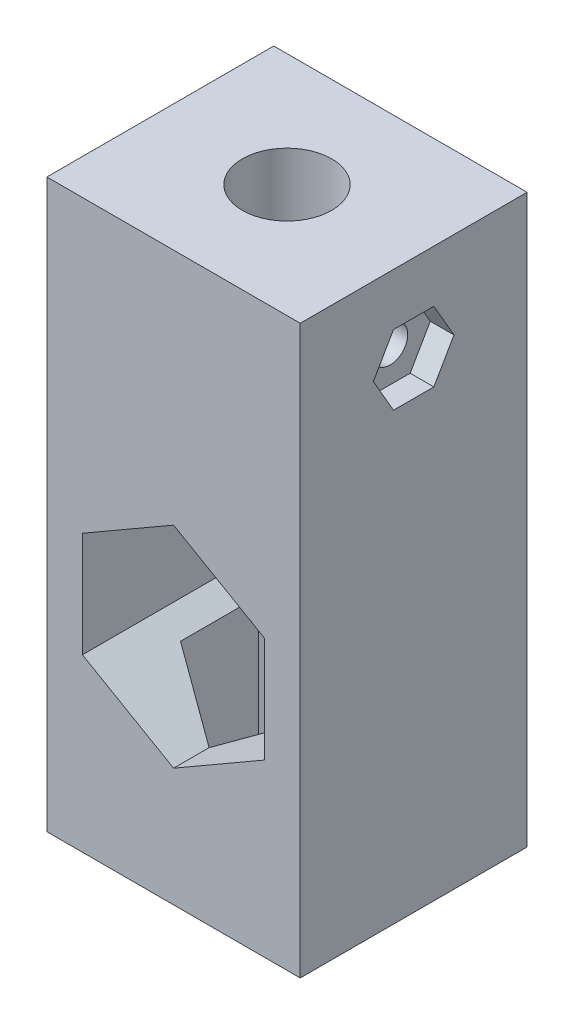
SolidWorks part; units mm, degrees
ref_plane "Plan de face" through (0, 0, 0) normal (0, 0, 1) x (1, 0, 0)
ref_plane "Plan de dessus" through (0, 0, 0) normal (0, 1, 0) x (1, 0, 0)
ref_plane "Plan de droite" through (0, 0, 0) normal (1, 0, 0) x (0, 0, -1)
sketch "Esquisse1" plane through (0, 0, 0) normal (0, 1, 0) x (1, 0, 0)
  line L0 (0, 0) -> (0, -9.5818) construction
  line L3 (-5.7, 3.2909) -> (-5.7, -3.2909) construction
  line L4 (-5.7, -3.2909) -> (0, -6.5818) construction
  line L7 (-5.7, 0) -> (-10.7, 0) construction
  line L8 (-10.7, 9.5818) -> (-10.7, -9.5818)
  line L9 (-5.7, 0) -> (0, 0) construction
  line L10 (-10.7, -9.5818) -> (10.7, -9.5818)
  line L11 (5.7, -3.2909) -> (0, -6.5818) construction
  line L12 (5.7, 3.2909) -> (5.7, -3.2909) construction
  line L13 (2.85, -4.9363) -> (5.7, -3.2909) [skipped]
  line L14 (5.7, 0) -> (5.7, 3.2909) [skipped]
  line L15 (2.85, 4.9363) -> (0, 6.5818) [skipped]
  line L16 (0, 6.5818) -> (-2.85, 4.9363) [skipped]
  line L17 (5.7, 0) -> (10.7, 0) construction
  line L18 (10.7, 9.5818) -> (10.7, -9.5818)
  line L19 (-5.7, 0) -> (5.7, 0) construction
  line L20 (-10.7, 9.5818) -> (10.7, 9.5818)
  line L21 (5.7, 3.2909) -> (0, 6.5818) construction
  line L22 (-5.7, 3.2909) -> (0, 6.5818) construction
  arc A0 (-5.7, 0) -> (0, -5.7) centre (0, 0) ccw construction
  dimension "D2" = 5.7
  dimension "D3" = 5
  dimension "D4" = 3
extrude "Boss.-Extru.1" add sketch "Esquisse1" along normal blind 47.9
sketch "Esquisse2" plane through (0, 0, 0) normal (0, -1, 0) x (-1, 0, 0)
  line L1 (5.7, -3.2909) -> (0, -6.5818)
  line L2 (0, -6.5818) -> (-5.7, -3.2909)
  line L4 (-5.7, 0) -> (5.7, 0) construction
  line L5 (-5.7, -3.2909) -> (-5.7, 3.2909)
  line L6 (-5.7, 3.2909) -> (0, 6.5818)
  line L7 (0, 6.5818) -> (5.7, 3.2909)
  line L8 (5.7, 3.2909) -> (5.7, -3.2909)
extrude "Enlèv. mat.-Extru.1" cut sketch "Esquisse2" against normal blind 32.9
sketch "Esquisse3" plane through (0, 47.9, 0) normal (0, 1, 0) x (1, 0, 0)
  line L1 (3.525, 0) -> (-3.525, 0) construction
  line L2 (-5.7, 0) -> (5.7, 0) construction
  circle A0 centre (0, 0) radius 3.525 construction
  circle A2 centre (0, 0) radius 3.775
  dimension "D1" = 7.05
  dimension "D2" = 0.25
extrude "Enlèv. mat.-Extru.2" cut sketch "Esquisse3" against normal up to next
sketch "Esquisse4" plane through (0, 0, 9.5818) normal (0, 0, 1) x (1, 0, 0)
  line L0 (-10.7, 47.9) -> (-10.7, 0) construction
  line L5 (0, 47.9) -> (0, 0) construction
  line L6 (-10.7, 47.9) -> (10.7, 47.9) construction
  line L21 (-7.7, 44.9) -> (7.7, 44.9) construction
  line L22 (0, 27.7824) -> (-7.7, 23.3368)
  line L23 (-7.7, 23.3368) -> (-7.7, 14.4456)
  line L24 (-7.7, 14.4456) -> (0, 10)
  line L25 (0, 10) -> (7.7, 14.4456)
  line L26 (7.7, 14.4456) -> (7.7, 23.3368)
  line L27 (7.7, 23.3368) -> (0, 27.7824)
  line L28 (-7.7, 44.9) -> (-7.7, 37.7824) construction
  line L29 (-7.7, 37.7824) -> (7.7, 37.7824) construction
  line L30 (7.7, 44.9) -> (7.7, 37.7824) construction
  circle A0 centre (0, 18.8912) radius 7.7 construction
  dimension "D1" = 10
  dimension "D2" = 3
  dimension "D3" = 10
  dimension "D4" = 3
extrude "Enlèv. mat.-Extru.3" cut sketch "Esquisse4" against normal through all both and the other way through all
sketch "Esquisse5" plane through (10.7, 0, 0) normal (1, 0, 0) x (0, 0, -1)
  line L0 (-9.5818, 47.9) -> (9.5818, 47.9) construction
  line L3 (0, 47.9) -> (0, 40.55) construction
  circle A2 centre (0, 40.55) radius 1.5
  dimension "D1" = 3
  dimension "D2" = 7.35
extrude "Enlèv. mat.-Extru.4" cut sketch "Esquisse5" against normal blind 16
sketch "Esquisse6" plane through (10.7, 0, 0) normal (1, 0, 0) x (0, 0, -1)
  line L1 (3.1177, 40.55) -> (1.5588, 43.25) construction
  line L2 (1.5588, 43.25) -> (-1.5588, 43.25) construction
  line L3 (-1.5588, 43.25) -> (-3.1177, 40.55) construction
  line L4 (-3.1177, 40.55) -> (-1.5588, 37.85) construction
  line L5 (-1.5588, 37.85) -> (1.5588, 37.85) construction
  line L6 (1.5588, 37.85) -> (3.1177, 40.55) construction
  line L26 (1.7032, 43.5) -> (-1.7032, 43.5)
  line L27 (-1.7032, 43.5) -> (-3.4064, 40.55)
  line L28 (-3.4064, 40.55) -> (-1.7032, 37.6)
  line L29 (-1.7032, 37.6) -> (1.7032, 37.6)
  line L30 (1.7032, 37.6) -> (3.4064, 40.55)
  line L31 (3.4064, 40.55) -> (1.7032, 43.5)
  circle A0 centre (0, 40.55) radius 2.7 construction
  circle A1 centre (0, 40.55) radius 1.5 construction
  circle A2 centre (0, 40.55) radius 2.95 construction
  dimension "D1" = 5.4
  dimension "D2" = 0.25
extrude "Enlèv. mat.-Extru.5" cut sketch "Esquisse6" against normal blind 2
